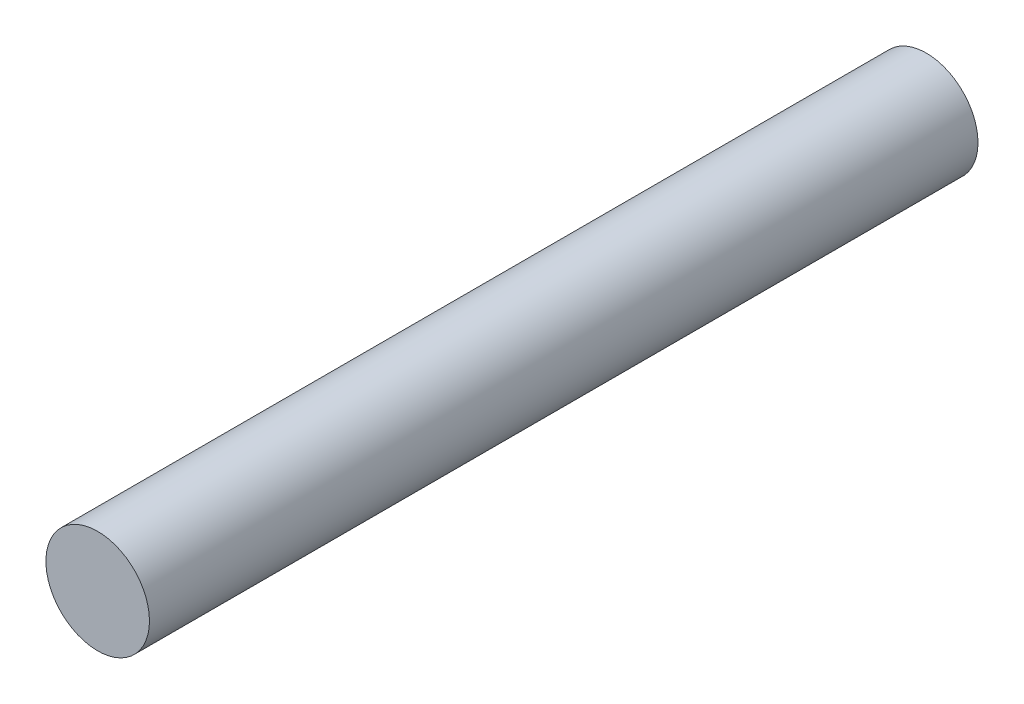
SolidWorks part; units mm, degrees
ref_plane "Front Plane" through (0, 0, 0) normal (0, 0, 1) x (1, 0, 0)
ref_plane "Top Plane" through (0, 0, 0) normal (0, 1, 0) x (1, 0, 0)
ref_plane "Right Plane" through (0, 0, 0) normal (1, 0, 0) x (0, 0, -1)
sketch "Esquisse1" plane through (0, 0, 0) normal (0, 0, 1) x (1, 0, 0)
  circle A0 centre (0, 0) radius 1.25
  dimension "D1" = 2.5
extrude "Boss.-Extru.1" add sketch "Esquisse1" along normal blind 20
